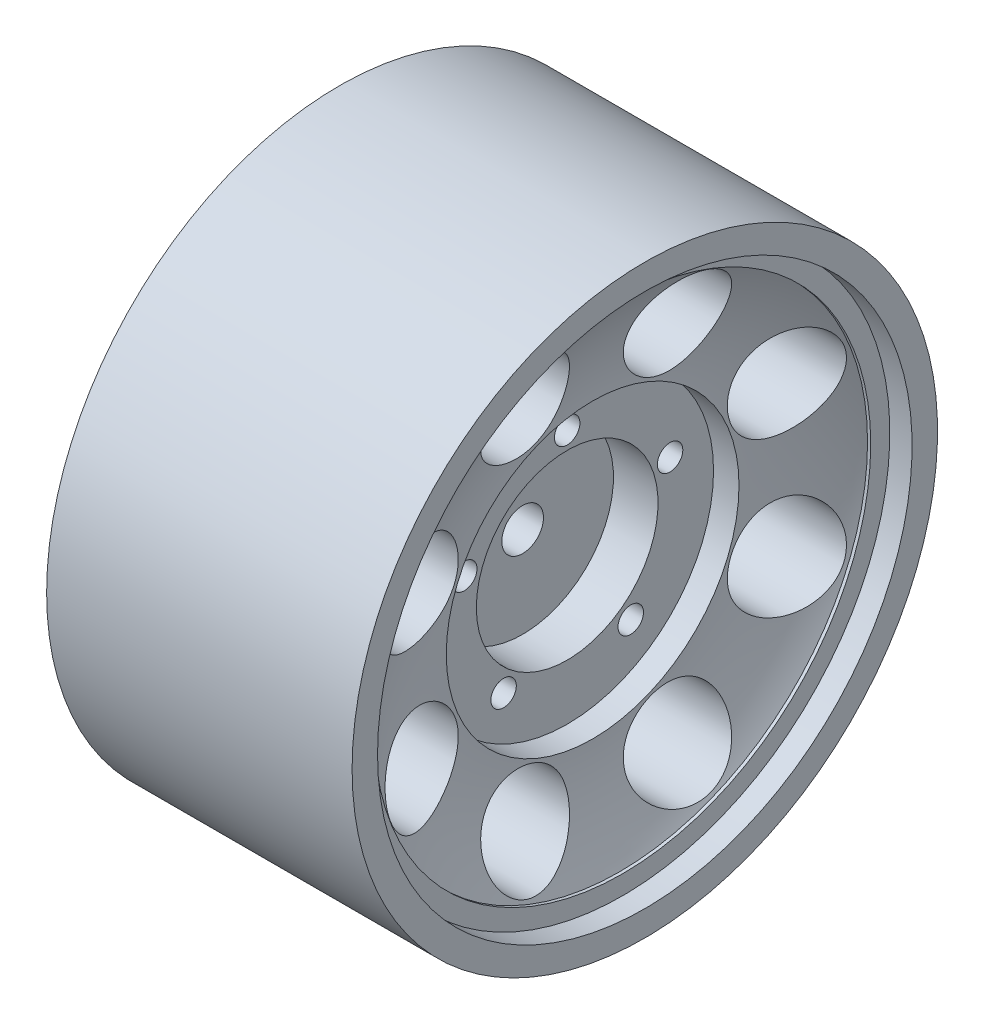
SolidWorks part; units mm, degrees
ref_plane "Front Plane" through (0, 0, 0) normal (0, 0, 1) x (1, 0, 0)
ref_plane "Top Plane" through (0, 0, 0) normal (0, 1, 0) x (1, 0, 0)
ref_plane "Right Plane" through (0, 0, 0) normal (1, 0, 0) x (0, 0, -1)
sketch "Sketch1" plane through (0, 0, 0) normal (0, 1, 0) x (1, 0, 0)
  line L0 (0, 0) -> (4.9, 0) construction
  line L1 (8.55, 1.6383) -> (8.55, 7.1383)
  line L2 (8.55, 7.1383) -> (12.05, 7.1383)
  line L3 (12.05, 7.1383) -> (12.05, 11.5)
  line L4 (12.05, 11.5) -> (14.05, 11.5)
  line L5 (16.15, 19.5) -> (16.4, 19.5)
  line L6 (16.4, 19.5) -> (16.4, 21)
  line L7 (16.4, 21) -> (18.15, 21)
  line L8 (18.15, 21) -> (18.15, 23)
  line L9 (18.15, 23) -> (-5.85, 23)
  line L10 (-5.85, 23) -> (-5.85, 21)
  line L11 (-5.85, 21) -> (-4.35, 19.5)
  line L12 (-4.35, 19.5) -> (7, 19.5)
  line L13 (7, 19.5) -> (7, 9.75)
  line L14 (7, 9.75) -> (0, 9.75)
  line L15 (0, 9.75) -> (0, 1.6383)
  line L16 (14.05, 11.5) -> (14.05, 23) construction
  line L17 (8.55, 1.6383) -> (0, 1.6383)
  arc A0 (14.05, 11.5) -> (16.15, 19.5) centre (30.3381, 11.5) cw
  dimension "D1" = 24
  dimension "D2" = 2
  dimension "D3" = 1.5
  dimension "D4" = 9.75
  dimension "D5" = 5.5
  dimension "D6" = 23
  dimension "D7" = 2
  dimension "D8" = 1.75
  dimension "D9" = 0.25
  dimension "D10" = 2
  dimension "D11" = 3.5
  dimension "D12" = 1.6383
  dimension "D13" = 45
  dimension "D14" = 7
  dimension "D15" = 12.85
  dimension "D16" = 2.1
  dimension "D17" = 8
revolve "Revolve1" add sketch "Sketch1" angle 360 about L0
sketch "Sketch2" plane through (0, 0, 0) normal (1, 0, 0) x (0, 0, -1)
  circle A0 centre (-5.9316, 14.3201) radius 3.75
  circle A1 centre (5.9316, 14.3201) radius 3.75
  circle A2 centre (14.3201, 5.9316) radius 3.75
  circle A3 centre (14.3201, -5.9316) radius 3.75
  circle A4 centre (5.9316, -14.3201) radius 3.75
  circle A5 centre (-5.9316, -14.3201) radius 3.75
  circle A6 centre (-14.3201, -5.9316) radius 3.75
  circle A7 centre (-14.3201, 5.9316) radius 3.75
  circle A8 centre (0, 0) radius 11.5 construction
  circle A9 centre (0, 0) radius 19.5 construction
  circle A10 centre (0, 0) radius 11.5 construction
  circle A11 centre (0, 0) radius 19.5 construction
  point P18 (0, 0)
  dimension "D2" = 7.5
  dimension "D3" = 15.5
  dimension "D1" = 8
extrude "Cut-Extrude2" cut sketch "Sketch2" against normal through all both and the other way through all
sketch "Sketch3" plane through (12.05, 0, 0) normal (1, 0, 0) x (0, 0, -1)
  circle A0 centre (0, 8.5) radius 1
  circle A1 centre (8.084, 2.6266) radius 1
  circle A2 centre (4.9962, -6.8766) radius 1
  circle A3 centre (-4.9962, -6.8766) radius 1
  circle A4 centre (-8.084, 2.6266) radius 1
  point P12 (0, 0)
  dimension "D3" = 2
  dimension "D2" = 8.5
  dimension "D1" = 5
extrude "Cut-Extrude3" cut sketch "Sketch3" against normal up to next
sketch "Sketch4" plane through (0, 0, 0) normal (-1, 0, 0) x (0, 0, 1)
  line L1 (6.9282, 0) -> (3.4641, 6)
  line L2 (3.4641, 6) -> (-3.4641, 6)
  line L3 (-3.4641, 6) -> (-6.9282, 0)
  line L4 (-6.9282, 0) -> (-3.4641, -6)
  line L5 (-3.4641, -6) -> (3.4641, -6)
  line L6 (3.4641, -6) -> (6.9282, 0)
  circle A0 centre (0, 0) radius 6 construction
  dimension "D1" = 12
extrude "Cut-Extrude4" cut sketch "Sketch4" against normal blind 6.148
